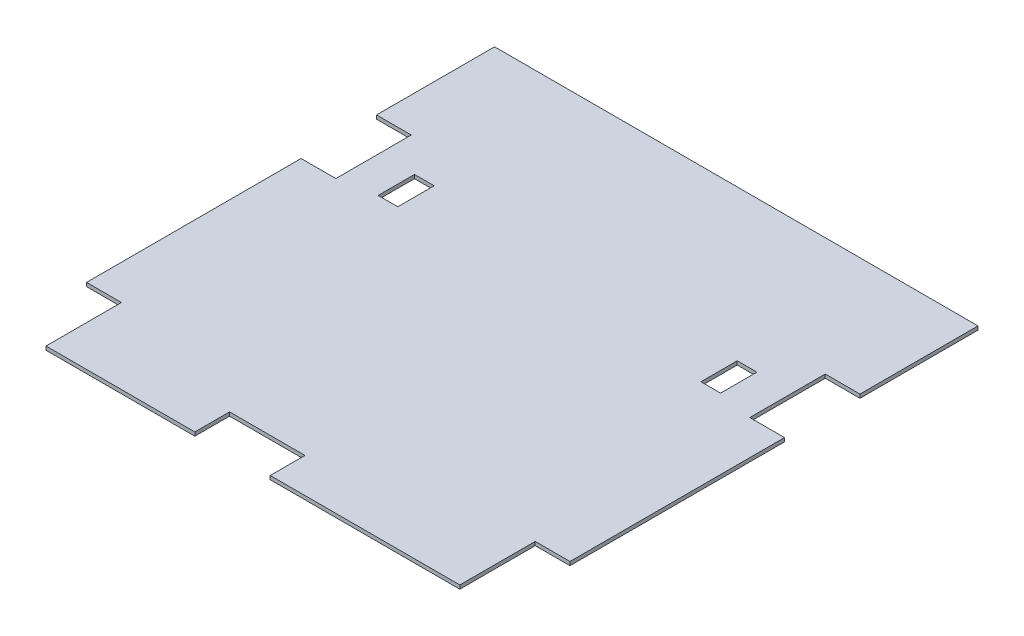
SolidWorks part; units mm, degrees
material "Custom Plastic"
ref_plane "Front Plane" through (0, 0, 0) normal (0, 0, 1) x (1, 0, 0)
ref_plane "Top Plane" through (0, 0, 0) normal (0, 1, 0) x (1, 0, 0)
ref_plane "Right Plane" through (0, 0, 0) normal (1, 0, 0) x (0, 0, -1)
sketch "Sketch1" plane through (0, 0, 0) normal (0, 1, 0) x (1, 0, 0)
  line L1 (0, 0) -> (416.08, 0)
  line L2 (0, 0) -> (0, 416.08)
  line L3 (0, 416.08) -> (416.08, 416.08)
  line L4 (416.08, 0) -> (416.08, 416.08)
extrude "Boss-Extrude1" add sketch "Sketch1" along normal blind 3.175 contours L2 L1 L4 L3
ref_plane "Plane1" through (208.04, 0, 0) normal (-1, 0, 0) x (0, 0, 1)
ref_plane "Plane2" through (0, 0, -208.04) normal (0, 0, -1) x (-1, 0, 0)
sketch "Sketch4" plane through (0, 0, 0) normal (0, -1, 0) x (1, 0, 0)
  line L0 (208.04, -416.08) -> (208.04, -105.878) construction
  line L1 (60.6819, -255.2052) -> (77.5962, -255.2052)
  line L2 (60.6819, -255.2052) -> (60.6819, -286.4642)
  line L3 (60.6819, -286.4642) -> (77.5962, -286.4642)
  line L4 (77.5962, -255.2052) -> (77.5962, -286.4642)
  line L5 (60.6819, -255.2052) -> (77.5962, -286.4642) construction
  line L6 (60.6819, -286.4642) -> (77.5962, -255.2052) construction
  line L7 (0, -416.08) -> (416.08, -416.08) construction
  line L8 (355.3981, -286.4642) -> (338.4838, -286.4642)
  line L9 (338.4838, -255.2052) -> (338.4838, -286.4642)
  line L10 (355.3981, -255.2052) -> (338.4838, -255.2052)
  line L11 (355.3981, -255.2052) -> (355.3981, -286.4642)
  line L12 (0, 0) -> (0, -416.08) construction
  line L13 (416.08, 0) -> (386.18, 0)
  line L14 (416.08, 0) -> (416.08, -64.9)
  line L15 (416.08, -64.9) -> (386.18, -64.9)
  line L16 (386.18, 0) -> (386.18, -64.9)
  line L17 (222.99, -29.9) -> (158.09, -29.9)
  line L18 (222.99, -29.9) -> (222.99, 0)
  line L19 (222.99, 0) -> (158.09, 0)
  line L20 (158.09, -29.9) -> (158.09, 0)
  line L21 (0, 0) -> (30, 0)
  line L22 (0, 0) -> (0, -64.9)
  line L23 (0, -64.9) -> (30, -64.9)
  line L24 (30, 0) -> (30, -64.9)
  line L25 (0, -314.48) -> (29.9, -314.48)
  line L26 (0, -314.48) -> (0, -249.58)
  line L27 (0, -249.58) -> (29.9, -249.58)
  line L28 (29.9, -314.48) -> (29.9, -249.58)
  line L29 (416.08, 0) -> (416.08, -416.08) construction
  line L30 (416.08, -249.58) -> (386.18, -249.58)
  line L31 (416.08, -249.58) -> (416.08, -314.48)
  line L32 (416.08, -314.48) -> (386.18, -314.48)
  line L33 (386.18, -249.58) -> (386.18, -314.48)
  line L34 (0, 0) -> (416.08, 0) construction
  point P0 (69.139, -270.8347)
  point P39 (73.6646, -271.1214)
  point P40 (81.8346, -276.4462)
  point P41 (83.7612, -278.758)
  point P42 (0, 0)
  point P43 (95.3205, -286.0789)
  point P44 (73.7431, -271.0518)
  point P45 (77.5962, -286.4642)
extrude "Cut-Extrude3" cut sketch "Sketch4" against normal through all
